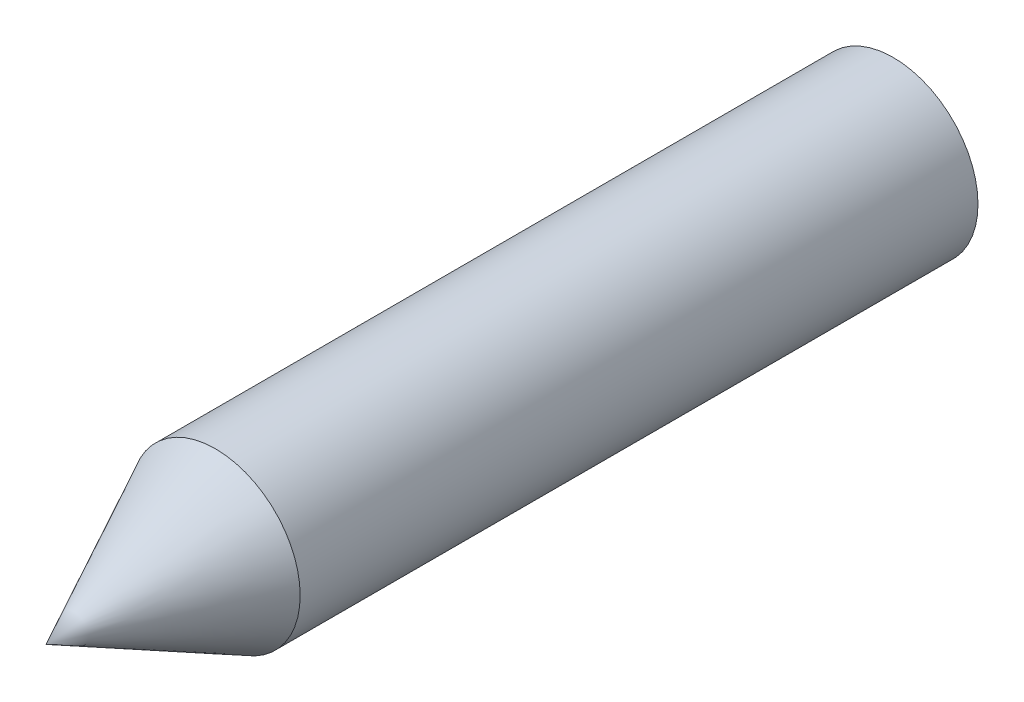
SolidWorks part; units mm, degrees
ref_plane "Front Plane" through (0, 0, 0) normal (0, 0, 1) x (1, 0, 0)
ref_plane "Top Plane" through (0, 0, 0) normal (0, 1, 0) x (1, 0, 0)
ref_plane "Right Plane" through (0, 0, 0) normal (1, 0, 0) x (0, 0, -1)
sketch "Sketch1" plane through (0, 0, 0) normal (0, 0, 1) x (1, 0, 0)
  circle A0 centre (0, 0) radius 5
  dimension "D1" = 10
extrude "Boss-Extrude1" add sketch "Sketch1" along normal blind 40
sketch "Sketch2" plane through (0, 0, 0) normal (0, 1, 0) x (1, 0, 0)
  line L0 (0, -40) -> (-5, -40)
  line L1 (0, -40) -> (0, -50)
  line L2 (-5, -40) -> (5, -40) construction
  line L3 (0, -50) -> (-5, -40)
  dimension "D1" = 10
revolve "Revolve1" add sketch "Sketch2" angle 360 about L1
